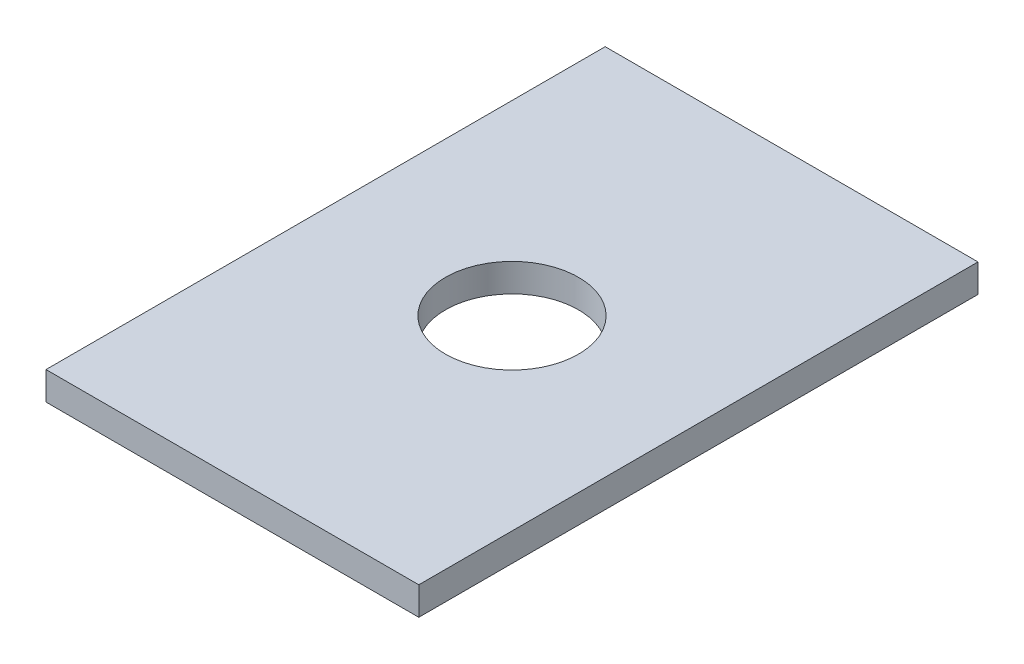
SolidWorks part; units mm, degrees
ref_plane "Front Plane" through (0, 0, 0) normal (0, 0, 1) x (1, 0, 0)
ref_plane "Top Plane" through (0, 0, 0) normal (0, 1, 0) x (1, 0, 0)
ref_plane "Right Plane" through (0, 0, 0) normal (1, 0, 0) x (0, 0, -1)
sketch "Sketch1" plane through (0, 0, 0) normal (0, 1, 0) x (1, 0, 0)
  line L0 (21, -31.5) -> (-21, 31.5) construction
  line L1 (21, -31.5) -> (-21, -31.5)
  line L2 (21, -31.5) -> (21, 31.5)
  line L3 (21, 31.5) -> (-21, 31.5)
  line L4 (-21, -31.5) -> (-21, 31.5)
  circle A0 centre (0, 0) radius 7.5
  dimension "D3" = 15
  dimension "D1" = 42
  dimension "D2" = 63
extrude "Boss-Extrude1" add sketch "Sketch1" along normal blind 3.175
